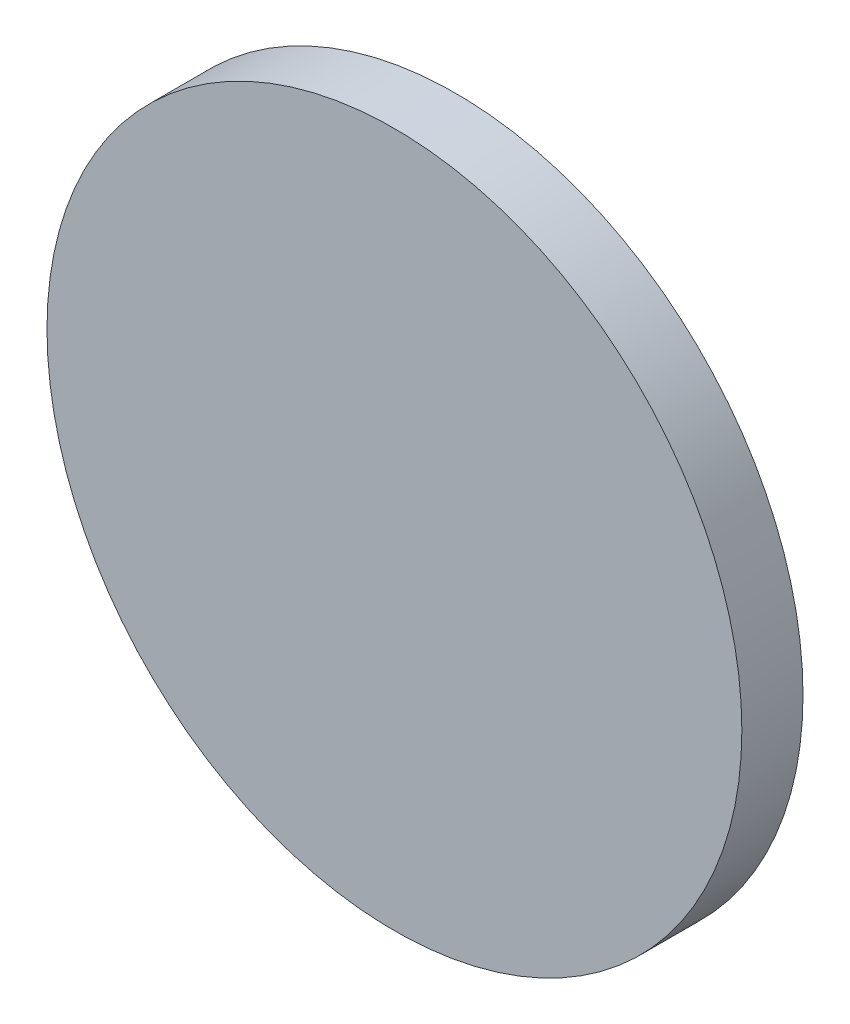
SolidWorks part; units mm, degrees
ref_plane "前视基准面" through (0, 0, 0) normal (0, 0, 1) x (1, 0, 0)
ref_plane "上视基准面" through (0, 0, 0) normal (0, 1, 0) x (1, 0, 0)
ref_plane "右视基准面" through (0, 0, 0) normal (1, 0, 0) x (0, 0, -1)
sketch "草图1" plane through (0, 0, 0) normal (0, 0, 1) x (1, 0, 0)
  circle A0 centre (0, 0) radius 6.25
  dimension "D1" = 12.5
extrude "凸台-拉伸1" add sketch "草图1" along normal blind 1.1
